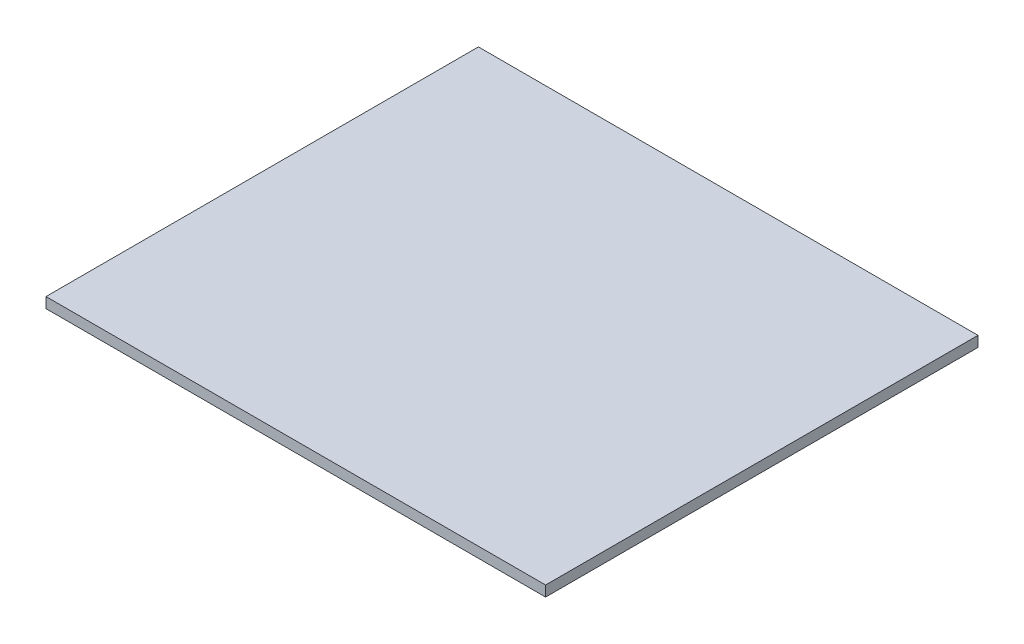
SolidWorks part; units mm, degrees
ref_plane "Front Plane" through (0, 0, 0) normal (0, 0, 1) x (1, 0, 0)
ref_plane "Top Plane" through (0, 0, 0) normal (0, 1, 0) x (1, 0, 0)
ref_plane "Right Plane" through (0, 0, 0) normal (1, 0, 0) x (0, 0, -1)
sketch "Sketch1" plane through (0, 0, 0) normal (0, 1, 0) x (1, 0, 0)
  line L1 (-59.5, -51.5) -> (59.5, -51.5)
  line L2 (-59.5, -51.5) -> (-59.5, 51.5)
  line L3 (-59.5, 51.5) -> (59.5, 51.5)
  line L4 (59.5, -51.5) -> (59.5, 51.5)
  line L5 (-59.5, -51.5) -> (59.5, 51.5) construction
  line L6 (-59.5, 51.5) -> (59.5, -51.5) construction
  point P0 (0, 0)
  dimension "D1" = 119
  dimension "D2" = 103
extrude "Boss-Extrude1" add sketch "Sketch1" along normal blind 2.5
